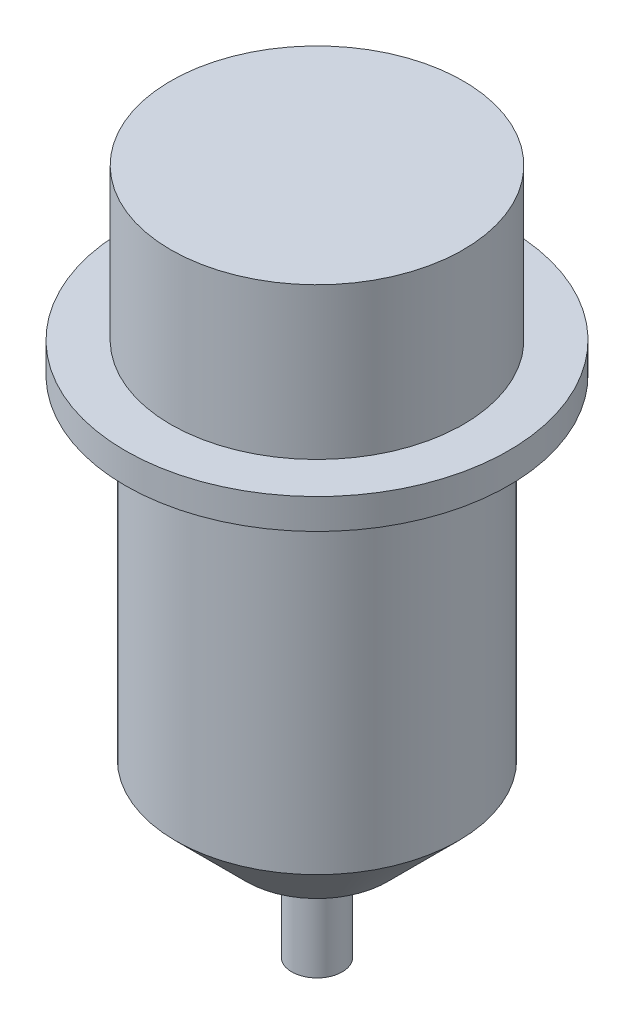
SolidWorks part; units mm, degrees
ref_plane "Спереди" through (0, 0, 0) normal (0, 0, 1) x (1, 0, 0)
ref_plane "Сверху" through (0, 0, 0) normal (0, 1, 0) x (1, 0, 0)
ref_plane "Справа" through (0, 0, 0) normal (1, 0, 0) x (0, 0, -1)
sketch "Эскиз1" plane through (0, 0, 0) normal (0, 1, 0) x (1, 0, 0)
  circle A0 centre (0, 0) radius 14
  dimension "D1" = 28
extrude "Бобышка-Вытянуть1" add sketch "Эскиз1" against normal blind 40
chamfer "Фаска1" distance 7 angle 45 1 edges at (0, -40, 14)
sketch "Эскиз2" plane through (0, 0, 0) normal (0, 1, 0) x (1, 0, 0)
  circle A0 centre (0, 0) radius 19
  dimension "D1" = 38
extrude "Бобышка-Вытянуть2" add sketch "Эскиз2" along normal blind 3
sketch "Эскиз3" plane through (0, 3, 0) normal (0, 1, 0) x (1, 0, 0)
  circle A0 centre (0, 0) radius 14.5
  dimension "D1" = 29
extrude "Бобышка-Вытянуть3" add sketch "Эскиз3" along normal blind 15
sketch "Эскиз4" plane through (0, -40, 0) normal (0, -1, 0) x (1, 0, 0)
  circle A0 centre (0, 0) radius 2.5
  dimension "D1" = 5
extrude "Бобышка-Вытянуть4" add sketch "Эскиз4" along normal blind 10
